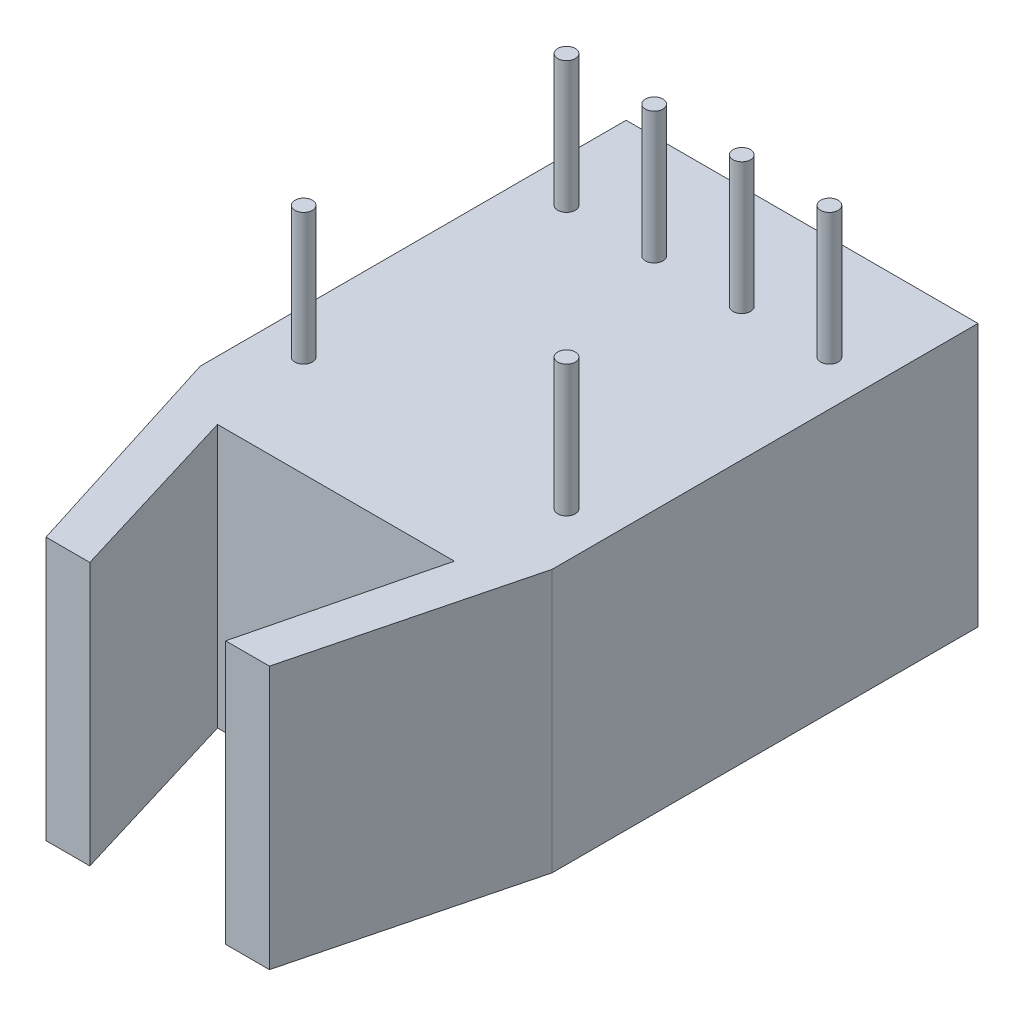
SolidWorks part; units mm, degrees
ref_plane "Front" through (0, 0, 0) normal (0, 0, 1) x (1, 0, 0)
ref_plane "Top" through (0, 0, 0) normal (0, 1, 0) x (1, 0, 0)
ref_plane "Right" through (0, 0, 0) normal (1, 0, 0) x (0, 0, -1)
sketch "HFBR Base" plane through (0, 0, 0) normal (0, 1, 0) x (1, 0, 0)
  line L1 (0, 0) -> (10.2, 0)
  line L2 (0, 0) -> (0, -12.3444)
  line L3 (0, -12.3444) -> (10.2, -12.3444)
  line L4 (10.2, 0) -> (10.2, -12.3444)
  dimension "D1" = 10.2
  dimension "D2" = 12.3444
extrude "Extrude1" add sketch "HFBR Base" along normal blind 7.62
sketch "Sketch2" plane through (0, 7.62, 0) normal (0, 1, 0) x (-1, 0, 0)
  line L0 (0, 12.3444) -> (-2.0567, 18.8722)
  line L1 (-2.0567, 18.8722) -> (-3.3267, 18.8722)
  line L2 (-3.3267, 18.8722) -> (-1.7138, 13.5575)
  line L3 (-1.7138, 13.5575) -> (-8.5796, 13.5575)
  line L4 (-8.5796, 13.5575) -> (-7.2637, 18.8722)
  line L5 (-7.2637, 18.8722) -> (-8.5337, 18.8722)
  line L6 (-8.5337, 18.8722) -> (-10.2, 12.3444)
  line L7 (-10.2, 12.3444) -> (0, 12.3444)
  dimension "D1" = 6.477
  dimension "D2" = 1.27
  dimension "D3" = 1.27
  dimension "D4" = 1.27
  dimension "D5" = 6.5278
  dimension "D6" = 1.27
extrude "Extrude2" add sketch "Sketch2" against normal blind 7.62
sketch "Sketch3" plane through (0, 7.62, 0) normal (0, 1, 0) x (-1, 0, 0)
  line L0 (0, 0) -> (0, 12.3444) construction
  line L1 (-10.2, 0) -> (0, 0) construction
  circle A0 centre (-1.27, 2.9972) radius 0.254
  dimension "D1" = 0.508
  dimension "D2" = 1.27
  dimension "D3" = 2.9972
extrude "Pins" add sketch "Sketch3" along normal blind 3.81
pattern_linear "LPattern1" count 4 spacing 2.54 along (1, 0, 0) count 2 spacing 7.62 along (0, 0, 1) skipping (1, 1), (2, 1) of "Pins"
